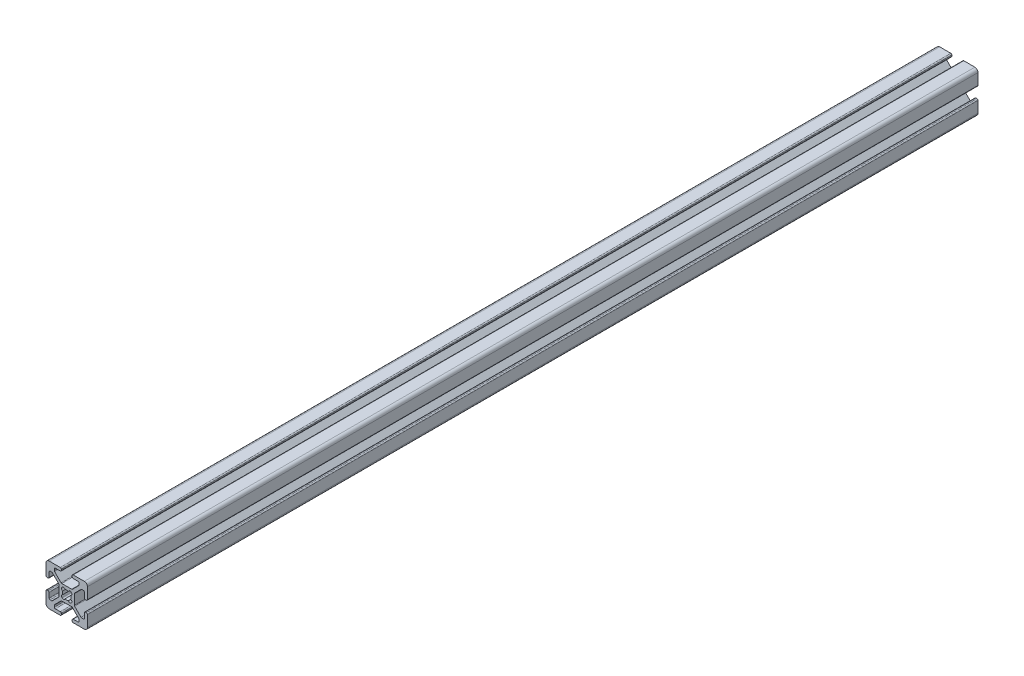
SolidWorks part; units mm, degrees
material "6105-T5 Aluminum"
ref_plane "Front Plane" through (0, 0, 0) normal (0, 0, 1) x (1, 0, 0)
ref_plane "Top Plane" through (0, 0, 0) normal (0, 1, 0) x (1, 0, 0)
ref_plane "Right Plane" through (0, 0, 0) normal (1, 0, 0) x (0, 0, -1)
sketch "Sketch1" plane through (0, 0, 0) normal (0, 0, 1) x (1, 0, 0)
  line L0 (9.492, 2.63) -> (9.008, 2.63)
  line L1 (8.5, 3.138) -> (8.5, 5.487)
  line L2 (10, 3.138) -> (10, 8.5)
  line L3 (3.655, -2.3839) -> (3.655, 2.3839)
  line L4 (7.2661, 5.995) -> (7.992, 5.995)
  line L5 (6.9069, 5.8462) -> (3.8038, 2.7431)
  line L6 (9.492, -2.63) -> (9.008, -2.63)
  line L7 (10, -3.138) -> (10, -8.5)
  line L8 (8.5, -3.138) -> (8.5, -5.487)
  line L9 (7.2661, -5.995) -> (7.992, -5.995)
  line L10 (6.9069, -5.8462) -> (3.8038, -2.7431)
  line L11 (2.1249, -2.3045) -> (2.3045, -2.1249)
  line L12 (-2.63, 9.492) -> (-2.63, 9.008)
  line L13 (-3.138, 10) -> (-8.5, 10)
  line L14 (-3.138, 8.5) -> (-5.487, 8.5)
  line L15 (2.3839, 3.655) -> (-2.3839, 3.655)
  line L16 (-5.995, 7.2661) -> (-5.995, 7.992)
  line L17 (-5.8462, 6.9069) -> (-2.7431, 3.8038)
  line L18 (2.63, 9.492) -> (2.63, 9.008)
  line L19 (3.138, 10) -> (8.5, 10)
  line L20 (3.138, 8.5) -> (5.487, 8.5)
  line L21 (5.995, 7.2661) -> (5.995, 7.992)
  line L22 (5.8462, 6.9069) -> (2.7431, 3.8038)
  line L23 (2.3045, 2.1249) -> (2.1249, 2.3045)
  line L24 (-9.492, -2.63) -> (-9.008, -2.63)
  line L25 (-10, -3.138) -> (-10, -8.5)
  line L26 (-8.5, -3.138) -> (-8.5, -5.487)
  line L27 (-3.655, 2.3839) -> (-3.655, -2.3839)
  line L28 (-7.2661, -5.995) -> (-7.992, -5.995)
  line L29 (-6.9069, -5.8462) -> (-3.8038, -2.7431)
  line L30 (-9.492, 2.63) -> (-9.008, 2.63)
  line L31 (-10, 3.138) -> (-10, 8.5)
  line L32 (-8.5, 3.138) -> (-8.5, 5.487)
  line L33 (-7.2661, 5.995) -> (-7.992, 5.995)
  line L34 (-6.9069, 5.8462) -> (-3.8038, 2.7431)
  line L35 (-2.1249, 2.3045) -> (-2.3045, 2.1249)
  line L36 (2.63, -9.492) -> (2.63, -9.008)
  line L37 (3.138, -10) -> (8.5, -10)
  line L38 (3.138, -8.5) -> (5.487, -8.5)
  line L39 (-2.3839, -3.655) -> (2.3839, -3.655)
  line L40 (5.995, -7.2661) -> (5.995, -7.992)
  line L41 (5.8462, -6.9069) -> (2.7431, -3.8038)
  line L42 (-2.63, -9.492) -> (-2.63, -9.008)
  line L43 (-3.138, -10) -> (-8.5, -10)
  line L44 (-3.138, -8.5) -> (-5.487, -8.5)
  line L45 (-5.995, -7.2661) -> (-5.995, -7.992)
  line L46 (-5.8462, -6.9069) -> (-2.7431, -3.8038)
  line L47 (-2.3045, -2.1249) -> (-2.1249, -2.3045)
  arc A0 (-0.804, -1.9351) -> (0.804, -1.9351) centre (0, 0) ccw
  arc A1 (8.5, 5.487) -> (7.992, 5.995) centre (7.992, 5.487) ccw
  arc A2 (7.2661, 5.995) -> (6.9069, 5.8462) centre (7.2661, 5.487) ccw
  arc A3 (3.8038, 2.7431) -> (3.655, 2.3839) centre (4.163, 2.3839) ccw
  arc A4 (3.655, -2.3839) -> (3.8038, -2.7431) centre (4.163, -2.3839) ccw
  arc A5 (6.9069, -5.8462) -> (7.2661, -5.995) centre (7.2661, -5.487) ccw
  arc A6 (7.992, -5.995) -> (8.5, -5.487) centre (7.992, -5.487) ccw
  arc A7 (9.008, -2.63) -> (8.5, -3.138) centre (9.008, -3.138) ccw
  arc A8 (10, -3.138) -> (9.492, -2.63) centre (9.492, -3.138) ccw
  arc A9 (9.492, 2.63) -> (10, 3.138) centre (9.492, 3.138) ccw
  arc A10 (8.5, 3.138) -> (9.008, 2.63) centre (9.008, 3.138) ccw
  arc A11 (0.804, -1.9351) -> (2.1249, -2.3045) centre (1.5684, -1.748) ccw
  arc A12 (2.3045, -2.1249) -> (1.9351, -0.804) centre (1.748, -1.5684) ccw
  arc A13 (-2.63, 9.492) -> (-3.138, 10) centre (-3.138, 9.492) ccw
  arc A14 (-3.138, 8.5) -> (-2.63, 9.008) centre (-3.138, 9.008) ccw
  arc A15 (1.9351, -0.804) -> (1.9351, 0.804) centre (0, 0) ccw
  arc A16 (-2.7431, 3.8038) -> (-2.3839, 3.655) centre (-2.3839, 4.163) ccw
  arc A17 (-5.487, 8.5) -> (-5.995, 7.992) centre (-5.487, 7.992) ccw
  arc A18 (-5.995, 7.2661) -> (-5.8462, 6.9069) centre (-5.487, 7.2661) ccw
  arc A19 (2.63, 9.008) -> (3.138, 8.5) centre (3.138, 9.008) ccw
  arc A20 (3.138, 10) -> (2.63, 9.492) centre (3.138, 9.492) ccw
  arc A21 (5.995, 7.992) -> (5.487, 8.5) centre (5.487, 7.992) ccw
  arc A22 (5.8462, 6.9069) -> (5.995, 7.2661) centre (5.487, 7.2661) ccw
  arc A23 (2.3839, 3.655) -> (2.7431, 3.8038) centre (2.3839, 4.163) ccw
  arc A24 (1.9351, 0.804) -> (2.3045, 2.1249) centre (1.748, 1.5684) ccw
  arc A25 (2.1249, 2.3045) -> (0.804, 1.9351) centre (1.5684, 1.748) ccw
  arc A26 (-9.492, -2.63) -> (-10, -3.138) centre (-9.492, -3.138) ccw
  arc A27 (-8.5, -3.138) -> (-9.008, -2.63) centre (-9.008, -3.138) ccw
  arc A28 (0.804, 1.9351) -> (-0.804, 1.9351) centre (0, 0) ccw
  arc A29 (-3.8038, -2.7431) -> (-3.655, -2.3839) centre (-4.163, -2.3839) ccw
  arc A30 (-8.5, -5.487) -> (-7.992, -5.995) centre (-7.992, -5.487) ccw
  arc A31 (-7.2661, -5.995) -> (-6.9069, -5.8462) centre (-7.2661, -5.487) ccw
  arc A32 (-9.008, 2.63) -> (-8.5, 3.138) centre (-9.008, 3.138) ccw
  arc A33 (-10, 3.138) -> (-9.492, 2.63) centre (-9.492, 3.138) ccw
  arc A34 (-7.992, 5.995) -> (-8.5, 5.487) centre (-7.992, 5.487) ccw
  arc A35 (-6.9069, 5.8462) -> (-7.2661, 5.995) centre (-7.2661, 5.487) ccw
  arc A36 (-3.655, 2.3839) -> (-3.8038, 2.7431) centre (-4.163, 2.3839) ccw
  arc A37 (-0.804, 1.9351) -> (-2.1249, 2.3045) centre (-1.5684, 1.748) ccw
  arc A38 (-2.3045, 2.1249) -> (-1.9351, 0.804) centre (-1.748, 1.5684) ccw
  arc A39 (2.63, -9.492) -> (3.138, -10) centre (3.138, -9.492) ccw
  arc A40 (3.138, -8.5) -> (2.63, -9.008) centre (3.138, -9.008) ccw
  arc A41 (-1.9351, 0.804) -> (-1.9351, -0.804) centre (0, 0) ccw
  arc A42 (2.7431, -3.8038) -> (2.3839, -3.655) centre (2.3839, -4.163) ccw
  arc A43 (5.487, -8.5) -> (5.995, -7.992) centre (5.487, -7.992) ccw
  arc A44 (5.995, -7.2661) -> (5.8462, -6.9069) centre (5.487, -7.2661) ccw
  arc A45 (-2.63, -9.008) -> (-3.138, -8.5) centre (-3.138, -9.008) ccw
  arc A46 (-3.138, -10) -> (-2.63, -9.492) centre (-3.138, -9.492) ccw
  arc A47 (-5.995, -7.992) -> (-5.487, -8.5) centre (-5.487, -7.992) ccw
  arc A48 (-5.8462, -6.9069) -> (-5.995, -7.2661) centre (-5.487, -7.2661) ccw
  arc A49 (-2.3839, -3.655) -> (-2.7431, -3.8038) centre (-2.3839, -4.163) ccw
  arc A50 (-1.9351, -0.804) -> (-2.3045, -2.1249) centre (-1.748, -1.5684) ccw
  arc A51 (-2.1249, -2.3045) -> (-0.804, -1.9351) centre (-1.5684, -1.748) ccw
  arc A52 (10, 8.5) -> (8.5, 10) centre (8.5, 8.5) ccw
  arc A53 (8.5, -10) -> (10, -8.5) centre (8.5, -8.5) ccw
  arc A54 (-10, -8.5) -> (-8.5, -10) centre (-8.5, -8.5) ccw
  arc A55 (-8.5, 10) -> (-10, 8.5) centre (-8.5, 8.5) ccw
extrude "Extrude1" add sketch "Sketch1" against normal blind 430
